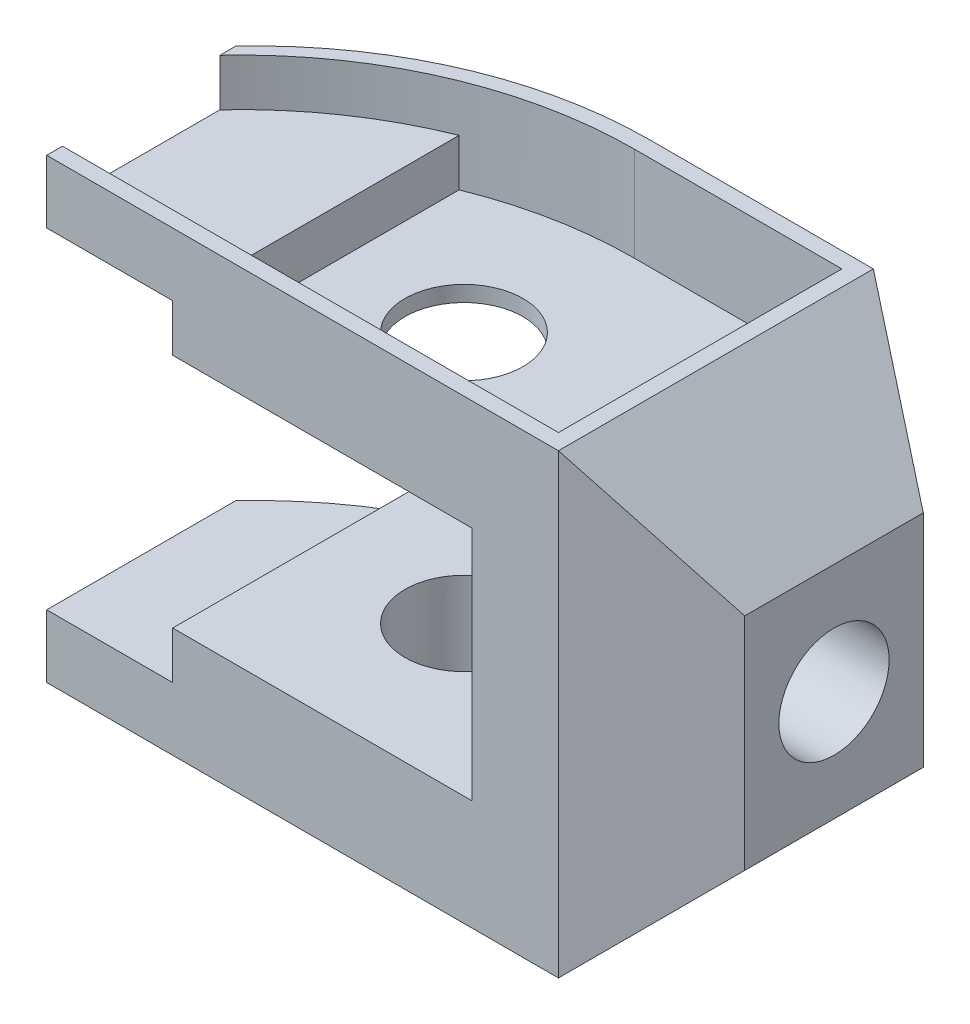
SolidWorks part; units mm, degrees
material "1060 Alloy"
ref_plane "Front Plane" through (0, 0, 0) normal (0, 0, 1) x (1, 0, 0)
ref_plane "Top Plane" through (0, 0, 0) normal (0, 1, 0) x (1, 0, 0)
ref_plane "Right Plane" through (0, 0, 0) normal (1, 0, 0) x (0, 0, -1)
sketch "Sketch1" plane through (0, 0, 0) normal (0, 1, 0) x (1, 0, 0)
  line L0 (0, -19) -> (0, 7.5) construction
  line L1 (-34, 0) -> (7.5, 0) construction
  line L2 (0, -19) -> (31, -19)
  line L3 (-34, -19) -> (-34, 5)
  line L4 (0, -19) -> (-34, -19)
  line L5 (31, -19) -> (46, -10.3397)
  line L6 (46, -10.3397) -> (46, 12.3397)
  line L7 (46, 12.3397) -> (31, 21)
  line L8 (31, 21) -> (2.6606, 21)
  line L9 (31, -19) -> (42.9903, -19) construction
  line L10 (31, 21) -> (42.9903, 21) construction
  circle A0 centre (0, 0) radius 7.5
  arc A1 (2.6606, 21) -> (-34, 5) centre (2.6606, -29) ccw
  point P4 (0, 0)
  point P10 (0, -19)
  point P19 (0, 0)
  point P20 (0, 0)
  point P21 (0, 0)
  dimension "D1" = 15
  dimension "D11" = 50
  dimension "D2" = 19
  dimension "D3" = 31
  dimension "D4" = 24
  dimension "D5" = 65
  dimension "D6" = 30
  dimension "D7" = 15
  dimension "D8" = 30
  dimension "D9" = 15
  dimension "D10" = 40
extrude "Boss-Extrude2" add sketch "Sketch1" along normal blind 58
sketch "Sketch4" plane through (0, 0, 0) normal (0, 0, 1) x (1, 0, 0)
  line L0 (31, 0) -> (46, 15)
  line L1 (46, 58) -> (46, 0) construction
  line L2 (46, 15) -> (46, 0)
  line L3 (46, 0) -> (31, 0)
  line L4 (31, 29) -> (46, 29) construction
  line L5 (31, 58) -> (31, 0) construction
  line L6 (31, 58) -> (46, 43)
  line L7 (46, 43) -> (46, 58)
  line L8 (46, 58) -> (31, 58)
  dimension "D1" = 45
extrude "Cut-Extrude1" cut sketch "Sketch4" against normal mid plane 58
sketch "Sketch6" plane through (0, 0, 0) normal (1, 0, 0) x (0, 0, -1)
  line L0 (-6, 29) -> (8, 29) construction
  line L3 (1, 36) -> (1, 22) construction
  line L8 (21, 58) -> (-19, 58) construction
  line L9 (-19, 58) -> (-19, 0) construction
  circle A0 centre (1, 29) radius 7
  dimension "D1" = 29
  dimension "D3" = 14
  dimension "D2" = 20
extrude "Cut-Extrude2" cut sketch "Sketch6" against normal mid plane 128
sketch "Sketch7" plane through (0, 0, 19) normal (0, 0, 1) x (1, 0, 0)
  line L0 (-1.5, 0) -> (-1.5, 58) construction
  line L1 (-34, 0) -> (31, 0) construction
  line L2 (-34, 58) -> (31, 58) construction
  line L3 (31, 29) -> (-34, 29) construction
  line L4 (31, 58) -> (31, 0) construction
  line L5 (-34, 58) -> (-34, 0) construction
  line L6 (-34, 50) -> (-18, 50)
  line L7 (-18, 50) -> (-18, 44)
  line L8 (-18, 44) -> (20, 44)
  line L9 (20, 44) -> (20, 14)
  line L10 (-18, 8) -> (-18, 14)
  line L11 (-18, 14) -> (20, 14)
  line L12 (-34, 8) -> (-18, 8)
  line L13 (-34, 50) -> (-34, 8)
  point P18 (20, 29)
  dimension "D1" = 8
  dimension "D2" = 6
  dimension "D3" = 16
  dimension "D4" = 11
extrude "Cut-Extrude3" cut sketch "Sketch7" against normal mid plane 128
sketch "Sketch8" plane through (0, 58, 0) normal (0, 1, 0) x (1, 0, 0)
  line L8 (29, 19) -> (2.6606, 19)
  line L10 (-34, -17) -> (29, -17)
  line L11 (29, 19) -> (29, -17)
  line L12 (31, 21) -> (31, -19) construction
  line L13 (31, 21) -> (2.6606, 21) construction
  line L14 (-34, 3) -> (-34, -17)
  line L15 (-34, -19) -> (31, -19) construction
  line L17 (-34, 5) -> (-34, -19) construction
  arc A0 (2.6606, 19) -> (-34, 3) centre (2.6606, -31) ccw
  arc A3 (2.6606, 21) -> (-34, 5) centre (2.6606, -29) ccw construction
  dimension "D3" = 2
  dimension "D2" = 50
  dimension "D1" = 2
  dimension "D4" = 2
  dimension "D5" = 2
extrude "Cut-Extrude7" cut sketch "Sketch8" against normal blind 6
sketch "Sketch11" plane through (0, 52, 0) normal (0, 1, 0) x (1, 0, 0)
  line L0 (-34, -17) -> (29, -17) construction
  line L1 (29, 19) -> (2.6606, 19) construction
  line L2 (29, -17) -> (29, 19) construction
  line L3 (-16, -17) -> (29, -17)
  line L4 (29, 19) -> (2.6606, 19)
  line L5 (29, -17) -> (29, 19)
  line L6 (-16, 15.3873) -> (-16, -17)
  line L7 (-34, 3) -> (-34, -17) construction
  arc A0 (2.6606, 19) -> (-34, 3) centre (2.6606, -31) ccw construction
  arc A1 (2.6606, 19) -> (-16, 15.3873) centre (2.6606, -31) ccw
  point P10 (-16, 15.3873)
  dimension "D1" = 18
extrude "Cut-Extrude8" cut sketch "Sketch11" against normal blind 6
equation "\"A\"= 58mm"
equation "\"B\"= 40mm"
equation "\"C\"= 65mm"
